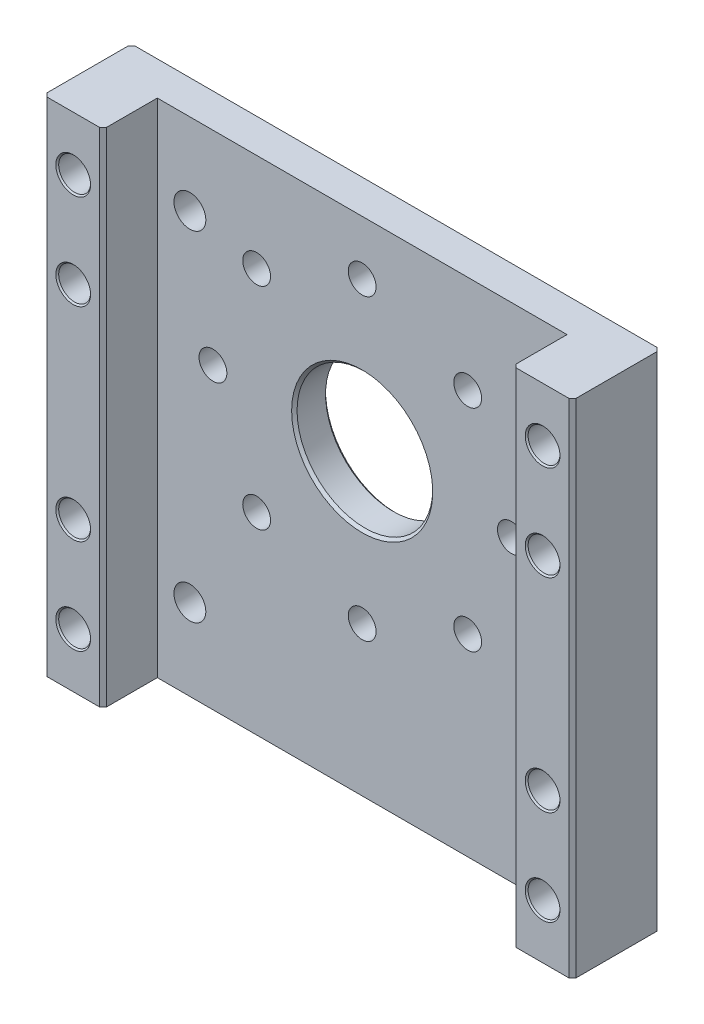
SolidWorks part; units mm, degrees
ref_plane "Front Plane" through (0, 0, 0) normal (0, 0, 1) x (1, 0, 0)
ref_plane "Top Plane" through (0, 0, 0) normal (0, 1, 0) x (1, 0, 0)
ref_plane "Right Plane" through (0, 0, 0) normal (1, 0, 0) x (0, 0, -1)
ref_plane "Plane1" through (0, 0, -17) normal (0, 0, 1) x (1, 0, 0)
sketch "Sketch1" plane through (0, 0, -17) normal (0, 0, 1) x (1, 0, 0)
  line L0 (19.5, 15) -> (-19.5, 15)
  line L1 (-19.5, 15) -> (-19.5, -22)
  line L2 (-19.5, -22) -> (19.5, -22)
  line L3 (19.5, -22) -> (19.5, 15)
extrude "Boss-Extrude1" add sketch "Sketch1" against normal blind 6.5
sketch "Sketch2" plane through (0, -22, 0) normal (0, -1, 0) x (1, 0, 0)
  line L0 (15.1, -17) -> (-15.1, -17)
  line L1 (-15.1, -17) -> (-15.1, -21)
  line L2 (-15.1, -21) -> (15.1, -21)
  line L3 (15.1, -21) -> (15.1, -17)
extrude "Cut-Extrude1" cut sketch "Sketch2" against normal through all
hole_wizard "Ø10.0 (10) Diameter Hole1" positions "Sketch4" profile "Sketch3" hole size "Ø10.0" standard "ANSI Metric"
sketch "Sketch4" plane through (0, 0, -21) normal (0, 0, 1) x (1, 0, 0)
  point P0 (0, 0)
sketch "Sketch3" plane through (0, 0, -21) normal (1, 0, 0) x (0, -1, 0)
  line L0 (0, 0) -> (0, 2.5)
  line L1 (0, 2.5) -> (5, 2.5)
  line L2 (5, 2.5) -> (5, 0)
  line L5 (5, 0) -> (0, 0)
  line L11 (0, -6.35) -> (0, 107.95) construction
  dimension "Thru Hole Dia." = 10
  dimension "Thru Hole Depth" = 2.5
hole_wizard "Ø2.05 (2.05) Diameter Hole1" positions "Sketch6" profile "Sketch5" hole size "Ø2.05" standard "ANSI Metric"
sketch "Sketch6" plane through (0, 0, -23.5) normal (0, 0, -1) x (-1, 0, 0)
  point P0 (-17.3, -18)
  point P1 (17.3, -18)
  point P2 (-17.3, -11)
  point P3 (17.3, -11)
sketch "Sketch5" plane through (17.3, -18, -23.5) normal (1, 0, 0) x (0, 1, 0)
  line L0 (0, 0) -> (0, 6.5)
  line L1 (0, 6.5) -> (1.025, 6.5)
  line L2 (1.025, 6.5) -> (1.025, 0)
  line L5 (1.025, 0) -> (0, 0)
  line L11 (0, -6.35) -> (0, 107.95) construction
  dimension "Thru Hole Dia." = 2.05
  dimension "Thru Hole Depth" = 6.5
hole_wizard "Ø2.05 (2.05) Diameter Hole2" positions "Sketch8" profile "Sketch7" hole size "Ø2.05" standard "ANSI Metric"
sketch "Sketch8" plane through (0, 0, -17) normal (0, 0, 1) x (1, 0, 0)
  point P0 (17.3, 4)
  point P1 (-17.3, 4)
  point P2 (17.3, 11)
  point P3 (-17.3, 11)
sketch "Sketch7" plane through (17.3, 4, -17) normal (1, 0, 0) x (0, -1, 0)
  line L0 (0, 0) -> (0, 6.5)
  line L1 (0, 6.5) -> (1.025, 6.5)
  line L2 (1.025, 6.5) -> (1.025, 0)
  line L5 (1.025, 0) -> (0, 0)
  line L11 (0, -6.35) -> (0, 107.95) construction
  dimension "Thru Hole Dia." = 2.05
  dimension "Thru Hole Depth" = 6.5
hole_wizard "Ø2.05 (2.05) Diameter Hole3" positions "Sketch10" profile "Sketch9" hole size "Ø2.05" standard "ANSI Metric"
sketch "Sketch10" plane through (0, 0, -23.5) normal (0, 0, -1) x (-1, 0, 0)
  point P0 (0, 11)
  point P1 (-7.7782, 7.7782)
  point P2 (-11, 0)
  point P3 (-7.7782, -7.7782)
  point P4 (0, -11)
  point P5 (7.7782, -7.7782)
  point P6 (11, 0)
  point P7 (7.7782, 7.7782)
  point P8 (13, 11)
  point P9 (-13, 11)
  point P10 (13, -17)
  point P11 (-13, -17)
sketch "Sketch9" plane through (0, 11, -23.5) normal (1, 0, 0) x (0, 1, 0)
  line L0 (0, 0) -> (0, 6.5)
  line L1 (0, 6.5) -> (1.025, 6.5)
  line L2 (1.025, 6.5) -> (1.025, 0)
  line L5 (1.025, 0) -> (0, 0)
  line L11 (0, -6.35) -> (0, 107.95) construction
  dimension "Thru Hole Dia." = 2.05
  dimension "Thru Hole Depth" = 6.5
chamfer "Chamfer1" distance 0.2562 angle 45 34 edges at (-14.025, 11, -23.5) (18.325, 4, -23.5) (-1.025, -11, -23.5) (-15.1, -3.5, -17) (18.325, 11, -23.5) (15.1, -3.5, -17) (19.5, -3.5, -17) (-12.025, 0, -23.5) (18.325, 4, -17) (-16.275, 4, -23.5) (16.275, -18, -17) (-16.275, 11, -23.5) (-16.275, 4, -17) (-14.025, -17, -23.5) (-18.325, -18, -17) (6.7532, -7.7782, -23.5) (18.325, 11, -17) (-8.8032, -7.7782, -23.5) (16.275, -11, -17) (-8.8032, 7.7782, -23.5) (-16.275, 11, -17) (16.275, -18, -23.5) (-18.325, -11, -17) (-18.325, -18, -23.5) (16.275, -11, -23.5) (-19.5, -3.5, -23.5) (-18.325, -11, -23.5) (19.5, -3.5, -23.5) (11.975, 11, -23.5) (-1.025, 11, -23.5) (11.975, -17, -23.5) (6.7532, 7.7782, -23.5) (-19.5, -3.5, -17) (9.975, 0, -23.5)
chamfer "Chamfer2" distance 0.1999 angle 45 2 edges at (5, 0, -23.5) (5, 0, -21)
ref_plane "Plane2" through (0, -3.5, 0) normal (0, 1, 0) x (1, 0, 0)
sketch "Sketch11" plane through (0, 0, -23.5) normal (0, 0, -1) x (-1, 0, 0)
  circle A0 centre (13, 11) radius 1.2812
  circle A1 centre (13, -17) radius 1.2812
  circle A2 centre (-13, -17) radius 1.2812
  circle A3 centre (-13, 11) radius 1.2812
  circle A4 centre (-13, 11) radius 1.2812 construction
extrude "Boss-Extrude3" add sketch "Sketch11" against normal up to surface (2.5 mm away) up to face at (-5.1999, 0, -21)
sketch "Sketch12" plane through (0, 0, -17) normal (0, 0, 1) x (1, 0, 0)
  line L0 (0, 0) -> (0, 17.3106) construction
  line L1 (21.7924, -3.5) -> (-23.3202, -3.5) construction
  line L2 (3.575, -3.5) -> (-3.575, -3.5) construction
  circle A0 centre (12.7, 9) radius 1.175
  circle A1 centre (-12.7, 9) radius 1.175
  circle A2 centre (12.7, -16) radius 1.175
  circle A3 centre (-12.7, -16) radius 1.175
  circle A4 centre (-17.3, -18) radius 1.175
  circle A5 centre (-17.3, -11) radius 1.175
  circle A6 centre (-17.3, 4) radius 1.175
  circle A7 centre (-17.3, 11) radius 1.175
  circle A8 centre (17.3, -18) radius 1.175
  circle A9 centre (17.3, -11) radius 1.175
  circle A10 centre (17.3, 4) radius 1.175
  circle A11 centre (17.3, 11) radius 1.175
  dimension "D3" = 2.35
  dimension "D1" = 25
  dimension "D2" = 25.4
extrude "Cut-Extrude2" cut sketch "Sketch12" against normal through all
